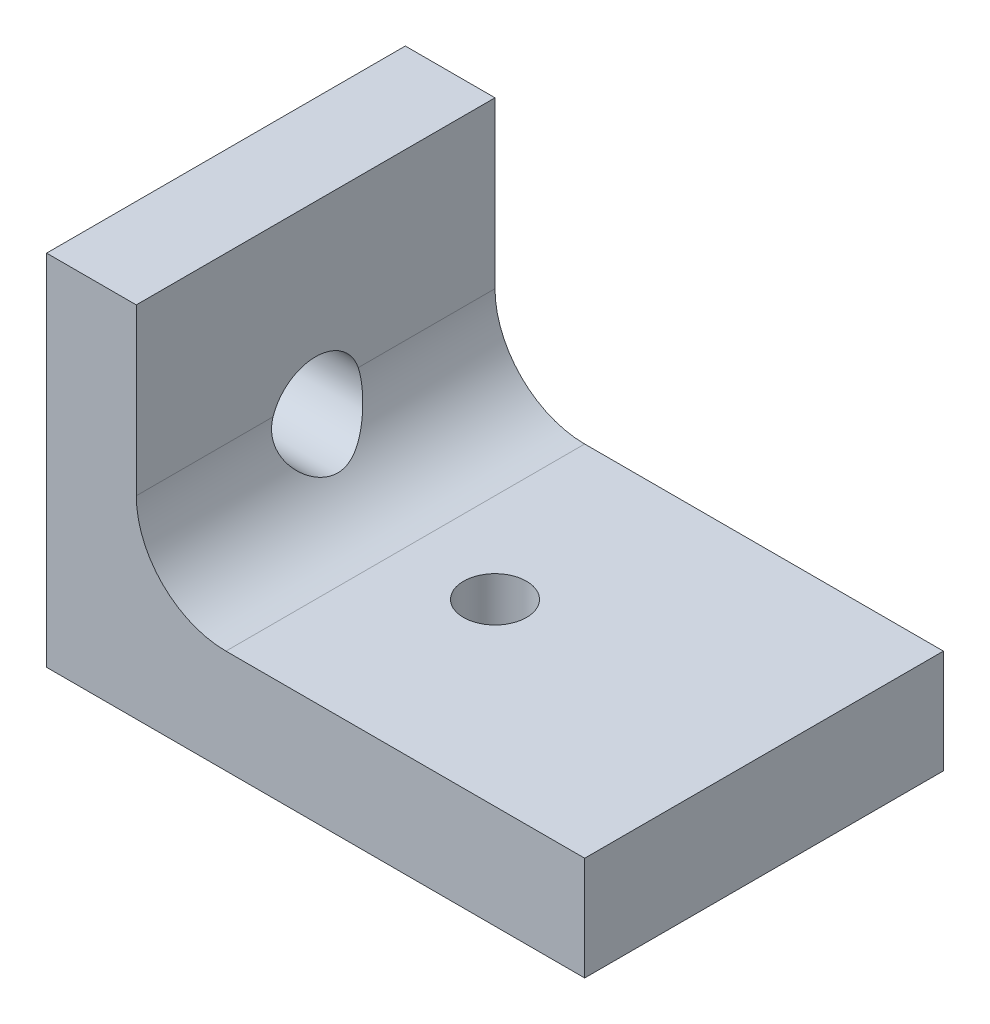
SolidWorks part; units mm, degrees
ref_plane "Front Plane" through (0, 0, 0) normal (0, 0, 1) x (1, 0, 0)
ref_plane "Top Plane" through (0, 0, 0) normal (0, 1, 0) x (1, 0, 0)
ref_plane "Right Plane" through (0, 0, 0) normal (1, 0, 0) x (0, 0, -1)
sketch "Sketch1" plane through (0, 0, 0) normal (0, 0, 1) x (1, 0, 0)
  line L0 (0, 20) -> (0, 0)
  line L1 (0, 0) -> (30, 0)
  line L2 (0, 20) -> (5, 20)
  line L3 (5, 20) -> (5, 10.7831)
  line L4 (10, 5.7831) -> (30, 5.7831)
  line L5 (30, 5.7831) -> (30, 0)
  arc A0 (5, 10.7831) -> (10, 5.7831) centre (10, 10.7831) ccw
  point P9 (5, 5.7831)
  dimension "D5" = 5
  dimension "D1" = 30
  dimension "D2" = 20
  dimension "D3" = 25
  dimension "D4" = 5
extrude "Boss-Extrude1" add sketch "Sketch1" along normal blind 20
sketch "Sketch2" plane through (0, 0, 0) normal (0, -1, 0) x (1, 0, 0)
  line L0 (0, 10) -> (30, 10) construction
  line L1 (0, 20) -> (0, 0) construction
  line L2 (30, 20) -> (30, 0) construction
  line L3 (15, 20) -> (15, 0) construction
  line L4 (0, 20) -> (30, 20) construction
  line L5 (0, 0) -> (30, 0) construction
  circle A0 centre (15, 10) radius 1.755
  dimension "D1" = 3.51
extrude "Cut-Extrude1" cut sketch "Sketch2" against normal blind 20
sketch "Sketch3" plane through (0, 0, 0) normal (-1, 0, 0) x (0, 0, 1)
  line L0 (10, 20) -> (10, 0) construction
  line L1 (20, 20) -> (0, 20) construction
  line L2 (20, 0) -> (0, 0) construction
  circle A0 centre (10, 10) radius 2.5
  dimension "D1" = 5
extrude "Cut-Extrude2" cut sketch "Sketch3" against normal blind 20
